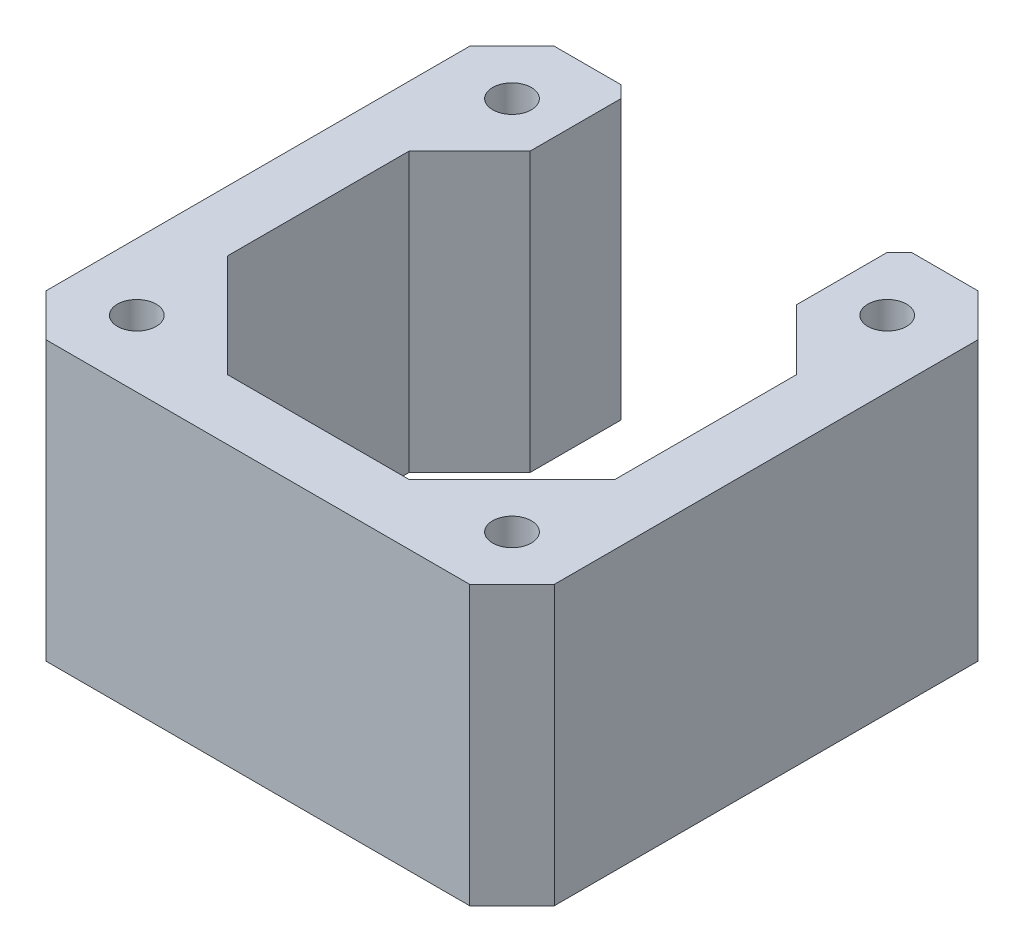
SolidWorks part; units mm, degrees
material "PET-G"
ref_plane "Спереди" through (0, 0, 0) normal (0, 0, 1) x (1, 0, 0)
ref_plane "Сверху" through (0, 0, 0) normal (0, 1, 0) x (1, 0, 0)
ref_plane "Справа" through (0, 0, 0) normal (1, 0, 0) x (0, 0, -1)
sketch "Sketch1" plane through (0, 0, 0) normal (0, 1, 0) x (1, 0, 0)
  line L0 (-16, -7.5) -> (-7.5, -16)
  line L1 (-7.5, -16) -> (7.5, -16)
  line L2 (-17.5, 21) -> (-21, 17.5)
  line L3 (-21, 17.5) -> (-21, -17.5)
  line L4 (-21, -17.5) -> (-17.5, -21)
  line L5 (-17.5, -21) -> (17.5, -21)
  line L6 (21, -17.5) -> (17.5, -21)
  line L7 (16, -7.5) -> (7.5, -16)
  line L8 (16, 7.5) -> (16, -7.5)
  line L9 (-17.5, 21) -> (-12, 21)
  line L10 (-16, 7.5) -> (-16, -7.5)
  line L11 (0, 0) -> (0, 30.1714) construction
  line L12 (-11, 20) -> (-11, 12.5)
  line L13 (-11, 12.5) -> (-16, 7.5)
  line L14 (21, 17.5) -> (21, -17.5)
  line L15 (17.5, 21) -> (21, 17.5)
  line L16 (17.5, 21) -> (12, 21)
  line L17 (11, 20) -> (11, 12.5)
  line L18 (11, 12.5) -> (16, 7.5)
  line L19 (-12, 21) -> (-11, 20)
  line L20 (12, 21) -> (11, 20)
  circle A0 centre (-15.5, 15.5) radius 1.6
  circle A1 centre (-15.5, -15.5) radius 1.6
  circle A2 centre (15.5, -15.5) radius 1.6
  circle A3 centre (15.5, 15.5) radius 1.6
  point P0 (-11, 21)
  point P37 (11, 21)
  dimension "D13" = 3.2
  dimension "D20" = 3.2
  dimension "D3" = 22
  dimension "D4" = 5
  dimension "D5" = 3.5
  dimension "D6" = 42
  dimension "D7" = 16
  dimension "D10" = 3.5
  dimension "D11" = 3.5
  dimension "D12" = 5
  dimension "D14" = 31
  dimension "D15" = 15.5
  dimension "D16" = 15
  dimension "D17" = 7.5
  dimension "D18" = 31
  dimension "D21" = 42
extrude "Base" add sketch "Sketch1" along normal blind 23 and the other way blind 0.0001
